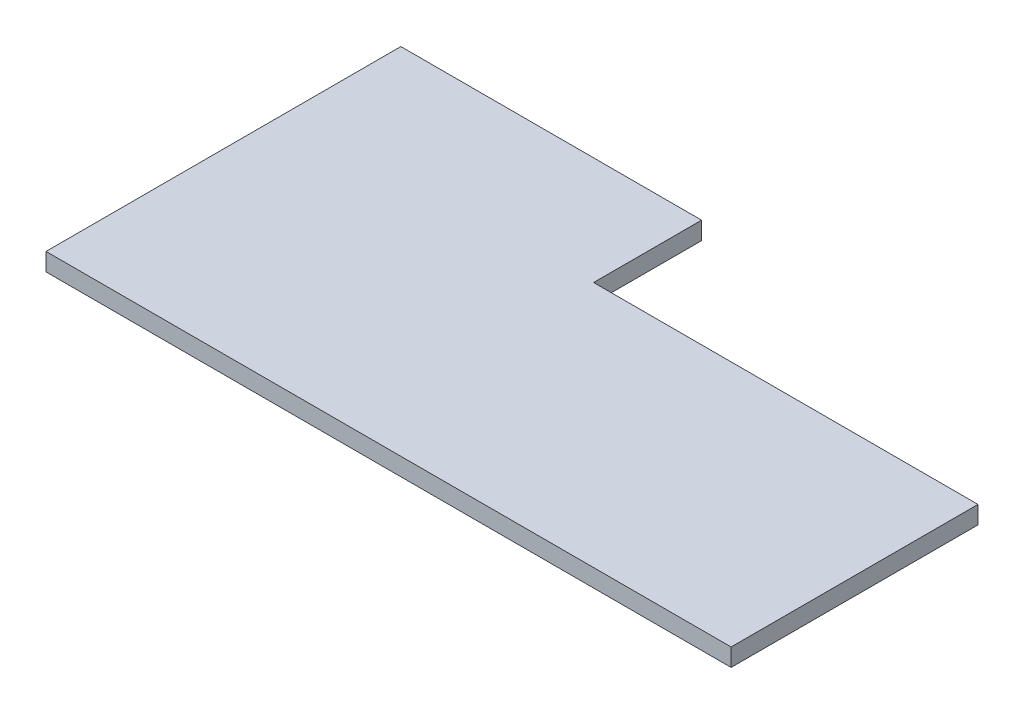
SolidWorks part; units mm, degrees
ref_plane "Front Plane" through (0, 0, 0) normal (0, 0, 1) x (1, 0, 0)
ref_plane "Top Plane" through (0, 0, 0) normal (0, 1, 0) x (1, 0, 0)
ref_plane "Right Plane" through (0, 0, 0) normal (1, 0, 0) x (0, 0, -1)
sketch "Sketch1" plane through (0, 0, 0) normal (0, 1, 0) x (1, 0, 0)
  line L0 (99.5034, -3.6822) -> (99.5034, -44.7322)
  line L1 (99.5034, -44.7322) -> (-14.4066, -44.7322)
  line L2 (-14.4066, -44.7322) -> (-14.4066, -0.7322)
  line L3 (-14.4066, -0.7322) -> (-14.4066, 14.2678)
  line L4 (-14.4066, 14.2678) -> (35.5934, 14.2678)
  line L5 (35.5934, 14.2678) -> (35.5934, -3.6822)
  line L6 (35.5934, -3.6822) -> (99.5034, -3.6822)
extrude "Boss-Extrude1" add sketch "Sketch1" along normal blind 2.95
